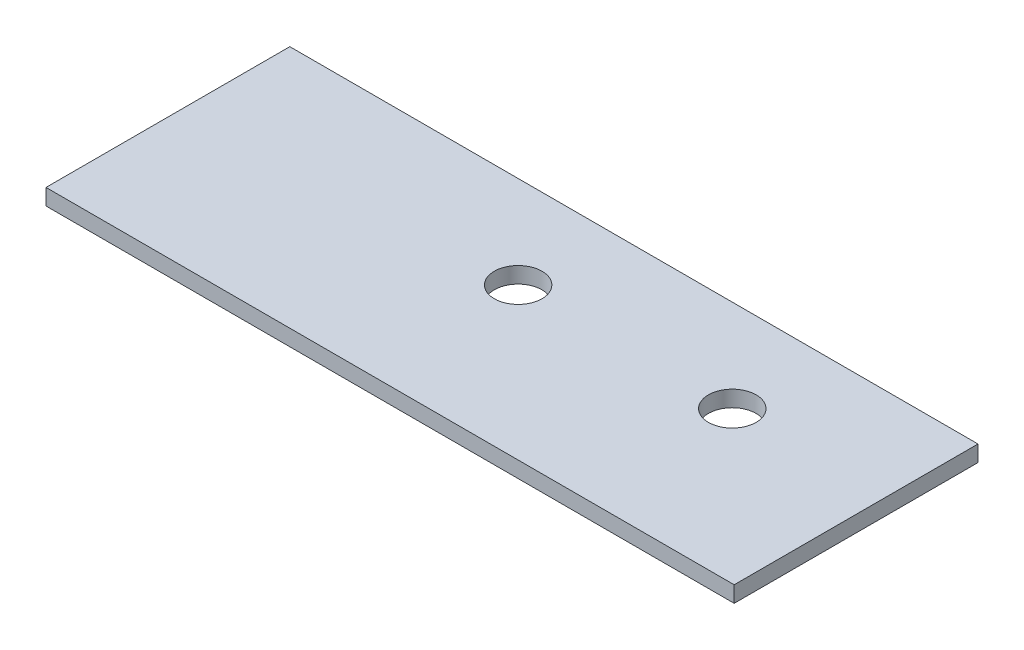
SolidWorks part; units mm, degrees
ref_plane "Front Plane" through (0, 0, 0) normal (0, 0, 1) x (1, 0, 0)
ref_plane "Top Plane" through (0, 0, 0) normal (0, 1, 0) x (1, 0, 0)
ref_plane "Right Plane" through (0, 0, 0) normal (1, 0, 0) x (0, 0, -1)
sketch "Sketch1" plane through (0, 0, 0) normal (0, 1, 0) x (1, 0, 0)
  line L1 (-16.23, 5.75) -> (16.23, 5.75)
  line L2 (-16.23, 5.75) -> (-16.23, -5.75)
  line L3 (-16.23, -5.75) -> (16.23, -5.75)
  line L4 (16.23, 5.75) -> (16.23, -5.75)
  line L5 (-16.23, 5.75) -> (16.23, -5.75) construction
  line L6 (-16.23, -5.75) -> (16.23, 5.75) construction
  circle A0 centre (-21.23, 0) radius 1.75 construction
  circle A4 centre (-1.11, 1.4) radius 1.125
  circle A5 centre (8.99, 1.4) radius 1.125
  point P0 (0, 0)
  dimension "D5" = 5
  dimension "D6" = 20.12
  dimension "D10" = 2.25
  dimension "D11" = 2.25
  dimension "D4" = 3.5
  dimension "D1" = 11.5
  dimension "D2" = 32.46
  dimension "D3" = 1.4
  dimension "D12" = 10.1
extrude "Boss-Extrude1" add sketch "Sketch1" along normal mid plane 0.76
